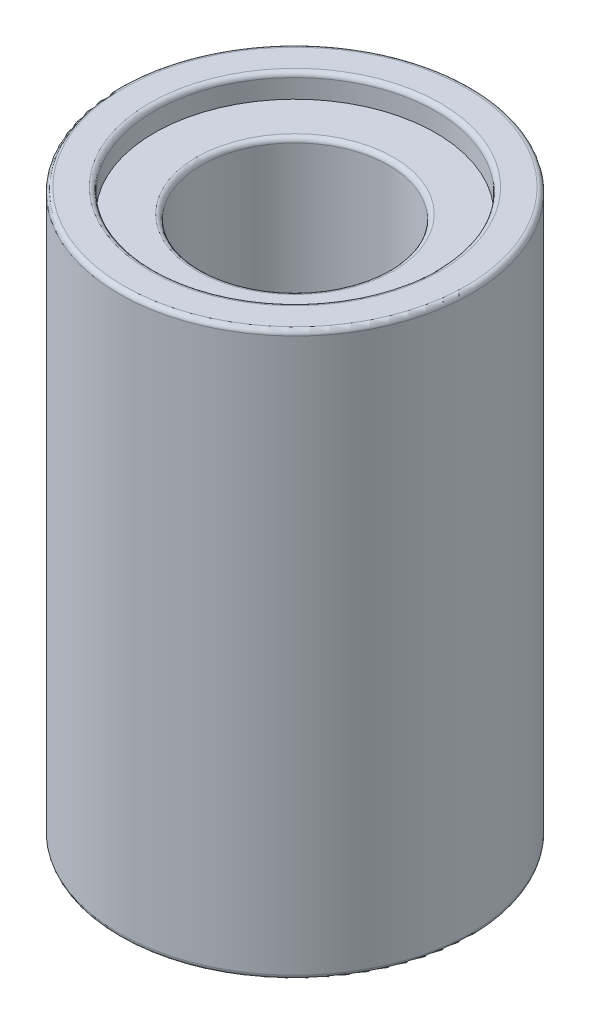
SolidWorks part; units mm, degrees
ref_plane "Front Plane" through (0, 0, 0) normal (0, 0, 1) x (1, 0, 0)
ref_plane "Top Plane" through (0, 0, 0) normal (0, 1, 0) x (1, 0, 0)
ref_plane "Right Plane" through (0, 0, 0) normal (1, 0, 0) x (0, 0, -1)
sketch "Sketch1" plane through (0, 0, 0) normal (0, 1, 0) x (1, 0, 0)
  circle A0 centre (0, 0) radius 7.5
  circle A1 centre (0, 0) radius 6
extrude "Boss-Extrude1" add sketch "Sketch1" along normal blind 24
ref_plane "Plane1" through (0, 23, 0) normal (0, 1, 0) x (1, 0, 0)
sketch "Sketch2" plane through (0, 23, 0) normal (0, 1, 0) x (1, 0, 0)
  circle A0 centre (0, 0) radius 6
  circle A1 centre (0, 0) radius 4
extrude "Boss-Extrude2" add sketch "Sketch2" against normal blind 22
fillet "Fillet1" radius 0.2 6 edges at (0, 24, 6) (0, 24, 7.5) (0, 0, 6) (0, 0, 7.5) (0, 1, 4) (0, 23, 4)
